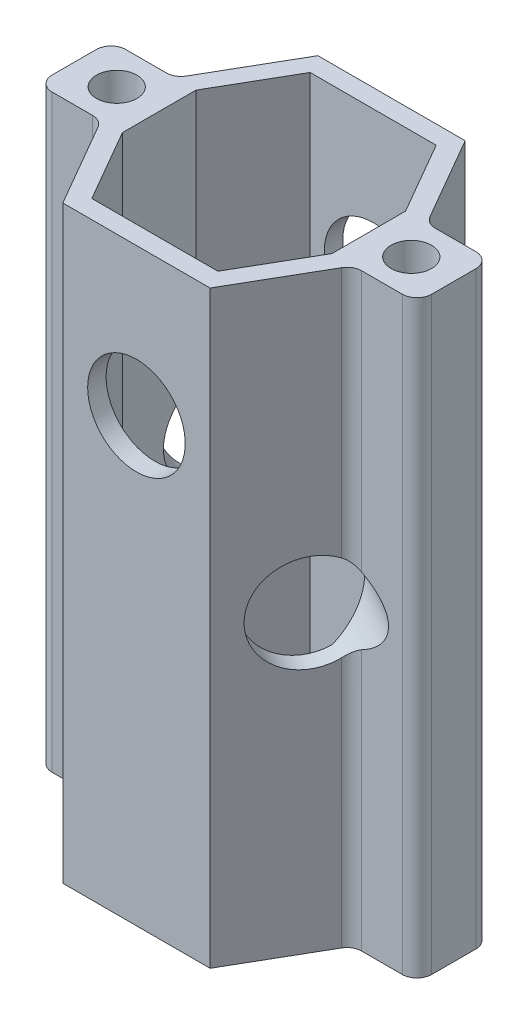
SolidWorks part; units mm, degrees
ref_plane "Front Plane" through (0, 0, 0) normal (0, 0, 1) x (1, 0, 0)
ref_plane "Top Plane" through (0, 0, 0) normal (0, 1, 0) x (1, 0, 0)
ref_plane "Right Plane" through (0, 0, 0) normal (1, 0, 0) x (0, 0, -1)
sketch "Sketch2" plane through (0, 0, 0) normal (0, 1, 0) x (1, 0, 0)
  line L0 (-12.7, 21.997) -> (12.7, 21.997)
  line L17 (12.7, 21.997) -> (25.4, 0)
  line L18 (25.4, 0) -> (12.7, -21.997)
  line L23 (12.7, -21.997) -> (-12.7, -21.997)
  line L24 (-12.7, -21.997) -> (-25.4, 0)
  line L25 (-25.4, 0) -> (-12.7, 21.997)
  line L26 (-10.8669, 18.822) -> (10.8669, 18.822)
  line L27 (10.8669, 18.822) -> (21.7338, 0)
  line L28 (21.7338, 0) -> (10.8669, -18.822)
  line L29 (10.8669, -18.822) -> (-10.8669, -18.822)
  line L30 (-10.8669, -18.822) -> (-21.7338, 0)
  line L31 (-21.7338, 0) -> (-10.8669, 18.822)
  line L32 (-25.4, 0) -> (25.4, 0) construction
  line L34 (-18.0677, -6.35) -> (-32.7323, -6.35)
  line L35 (-18.0677, -6.35) -> (-18.0677, 6.35)
  line L36 (-18.0677, 6.35) -> (-32.7323, 6.35)
  line L37 (-32.7323, -6.35) -> (-32.7323, 6.35)
  line L38 (-18.0677, -6.35) -> (-32.7323, 6.35) construction
  line L39 (-18.0677, 6.35) -> (-32.7323, -6.35) construction
  line L40 (18.0677, -6.35) -> (32.7323, -6.35)
  line L41 (18.0677, -6.35) -> (18.0677, 6.35)
  line L42 (18.0677, 6.35) -> (32.7323, 6.35)
  line L43 (32.7323, -6.35) -> (32.7323, 6.35)
  line L44 (18.0677, -6.35) -> (32.7323, 6.35) construction
  line L45 (18.0677, 6.35) -> (32.7323, -6.35) construction
  circle A0 centre (25.4, 0) radius 3.4925
  circle A1 centre (-25.4, 0) radius 3.4925
  point P0 (0, 0)
  point P3 (0, 21.997)
  point P5 (0, 0)
  point P20 (0, 0)
  dimension "D1" = 25.4
  dimension "D2" = 120
  dimension "D4" = 6.985
  dimension "D3" = 3.175
  dimension "D5" = 50.8
  dimension "D6" = 12.7
extrude "Boss-Extrude1" add sketch "Sketch2" along normal blind 101.6 contours A1 L25 L36 L37 L34 L24 | A0 L18 L40 L43 L42 L17 | L27 L42 L17 L0 L25 L36 L31 L26 | L40 L28 L29 L30 L34 L24 L23 L18 | A1 L24 L34 L30 L31 L36 L25 | L30 L35 L31 | A0 L17 L42 L27 L28 L40 L18 | L41 L28 L27
fillet "Fillet1" radius 2.54 8 edges at (-21.7338, 50.8, -6.35) (-32.7323, 50.8, -6.35) (-32.7323, 50.8, 6.35) (-21.7338, 50.8, 6.35) (21.7338, 50.8, 6.35) (32.7323, 50.8, 6.35) (32.7323, 50.8, -6.35) (21.7338, 50.8, -6.35)
sketch "Sketch11" plane through (0, 0, -21.997) normal (0, 0, -1) x (-1, 0, 0)
  line L0 (12.7, 101.6) -> (-12.7, 101.6) construction
  circle A0 centre (0, 76.2) radius 8.4137
  point P5 (0, 101.6)
  dimension "D2" = 16.8275
  dimension "D1" = 25.4
extrude "Cut-Extrude8" cut sketch "Sketch11" against normal through all both and the other way through all
sketch "Sketch12" plane through (-19.05, 0, -10.9985) normal (-0.866, 0, -0.5) x (-0.5, 0, 0.866)
  line L0 (3.9012, 101.6) -> (-12.7, 101.6) construction
  line L1 (-12.7, 101.6) -> (-12.7, 0) construction
  circle A0 centre (0, 50.8) radius 8.4137
  dimension "D2" = 16.8275
  dimension "D1" = 50.8
  dimension "D3" = 12.7
extrude "Cut-Extrude9" cut sketch "Sketch12" against normal through all both and the other way through all
sketch "Sketch13" plane through (19.05, 0, -10.9985) normal (0.866, 0, -0.5) x (-0.5, 0, -0.866)
  line L0 (12.7, 101.6) -> (-3.9012, 101.6) construction
  line L1 (12.7, 101.6) -> (12.7, 0) construction
  circle A0 centre (0, 25.4) radius 8.4138
  dimension "D1" = 16.8275
  dimension "D2" = 76.2
  dimension "D3" = 12.7
extrude "Cut-Extrude10" cut sketch "Sketch13" against normal through all both and the other way through all
